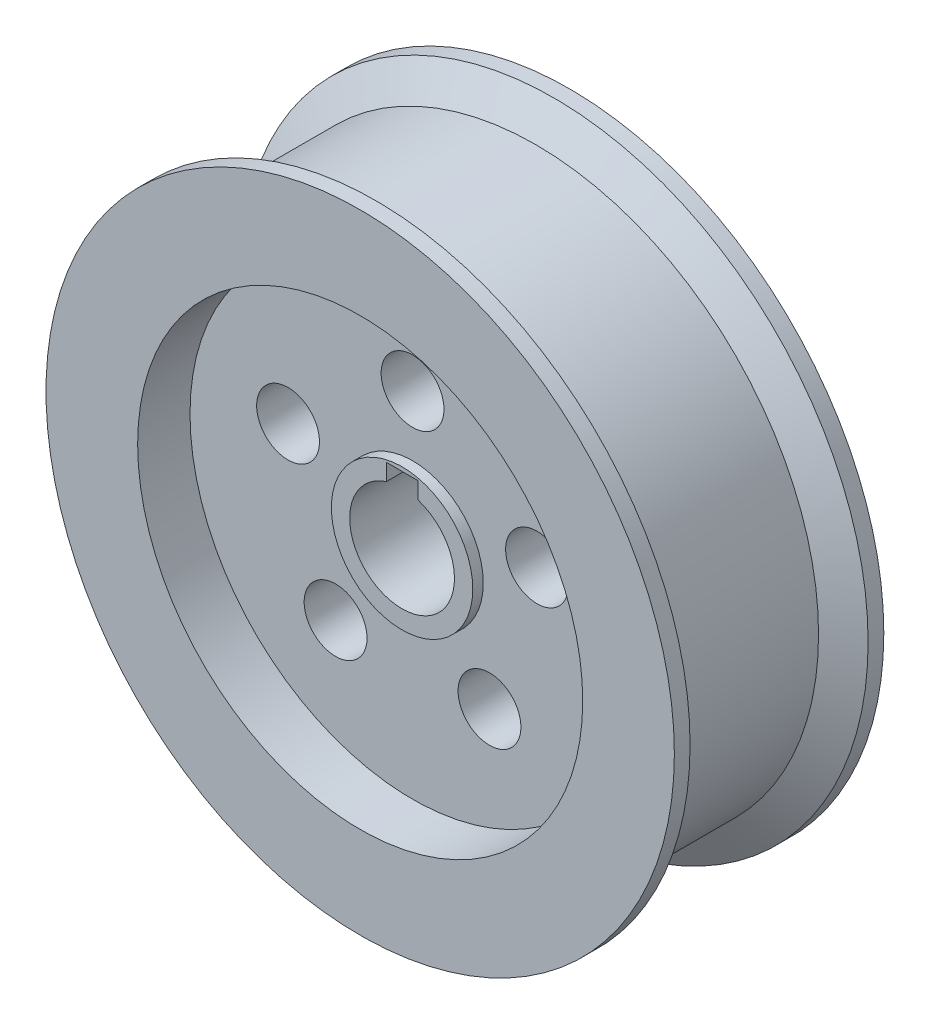
SolidWorks part; units mm, degrees
ref_plane "Front Plane" through (0, 0, 0) normal (0, 0, 1) x (1, 0, 0)
ref_plane "Top Plane" through (0, 0, 0) normal (0, 1, 0) x (1, 0, 0)
ref_plane "Right Plane" through (0, 0, 0) normal (1, 0, 0) x (0, 0, -1)
sketch "Sketch2" plane through (0, 0, 0) normal (0, 0, 1) x (1, 0, 0)
  circle A0 centre (0, 0) radius 60
  circle A1 centre (0, 0) radius 10
  dimension "D1" = 120
  dimension "D2" = 20
extrude "Boss-Extrude1" add sketch "Sketch2" along normal mid plane 40
sketch "Sketch3" plane through (0, 0, 20) normal (0, 0, 1) x (1, 0, 0)
  circle A0 centre (0, 0) radius 42.5
  dimension "D1" = 85
extrude "Cut-Extrude1" cut sketch "Sketch3" against normal blind 10
mirror "Mirror2" about plane through (0, 0, 0) normal (0, 0, 1) of "Cut-Extrude1"
sketch "Sketch4" plane through (0, 0, 10) normal (0, 0, 1) x (1, 0, 0)
  circle A0 centre (0, 25) radius 6
  dimension "D1" = 12
  dimension "D2" = 25
extrude "Cut-Extrude2" cut sketch "Sketch4" against normal through all both and the other way through all
pattern_circular "CirPattern2" count 5 over 360 about axis through (0, 0, 0) along (0, 0, 1) of "Cut-Extrude2"
sketch "Sketch5" plane through (0, 0, 0) normal (0, 1, 0) x (1, 0, 0)
  line L0 (0, 0) -> (0, 28.6742) construction
  line L1 (54, 13.5359) -> (60, 17)
  line L2 (60, -20) -> (60, 20) construction
  line L3 (60, 17) -> (60, -17)
  line L4 (60, -17) -> (54, -13.5359)
  line L5 (54, -13.5359) -> (54, 13.5359)
  line L6 (60, 20) -> (-60, 20) construction
  line L7 (-60, -20) -> (60, -20) construction
  dimension "D1" = 6
  dimension "D2" = 3
  dimension "D3" = 3
  dimension "D4" = 60
  dimension "D5" = 60
revolve "Cut-Revolve1" cut sketch "Sketch5" angle 360 about L0
sketch "Sketch6" plane through (0, 0, 10) normal (0, 0, 1) x (1, 0, 0)
  circle A0 centre (0, 0) radius 13.5
  circle A1 centre (0, 0) radius 10 construction
  circle A2 centre (0, 0) radius 10
  dimension "D1" = 27
extrude "Boss-Extrude3" add sketch "Sketch6" along normal blind 2 and the other way blind 7
sketch "Sketch8" plane through (0, 0, -10) normal (0, 0, -1) x (-1, 0, 0)
  line L1 (-3, 9.5169) -> (3, 9.5169)
  line L2 (-3, 9.5169) -> (-3, 12.7269)
  line L3 (-3, 12.7269) -> (3, 12.7269)
  line L4 (3, 9.5169) -> (3, 12.7269)
  line L5 (-3, 9.5169) -> (3, 12.7269) construction
  line L6 (-3, 12.7269) -> (3, 9.5169) construction
  point P0 (0, 11.1219)
  point P5 (0, 0)
  dimension "D1" = 3.21
  dimension "D2" = 6
extrude "Cut-Extrude3" cut sketch "Sketch8" against normal through all both and the other way through all
